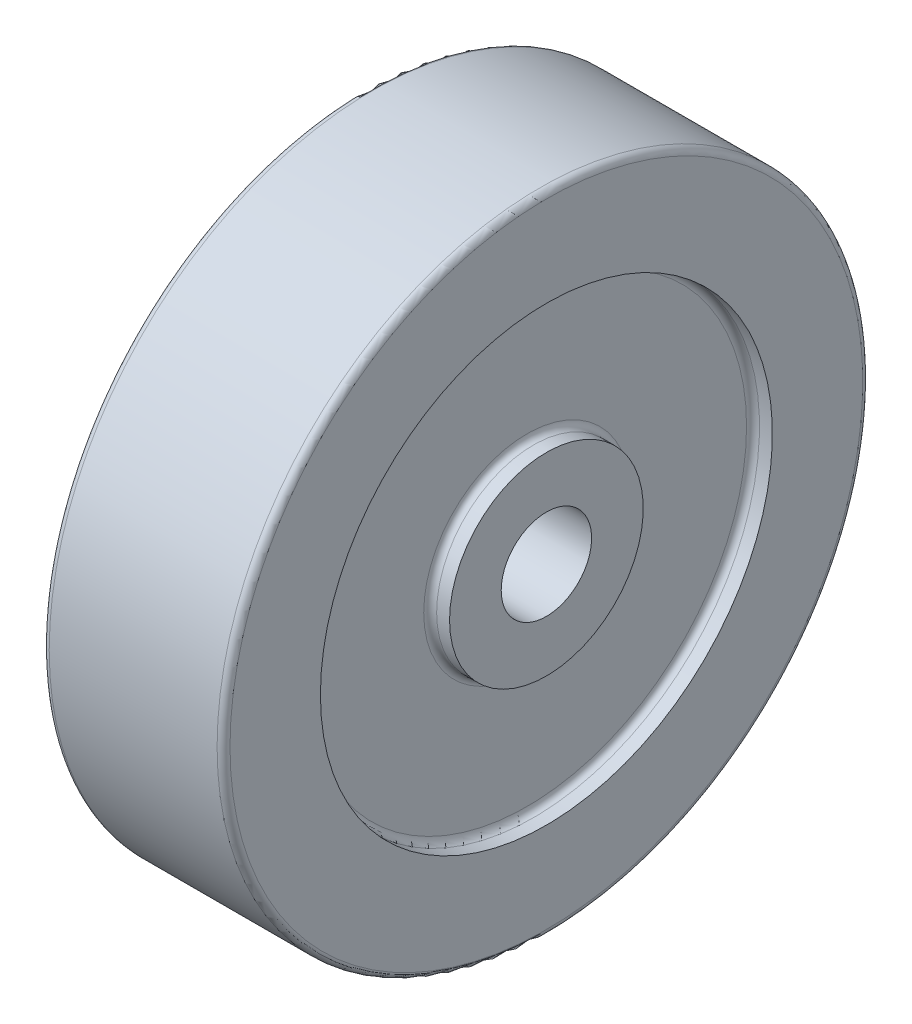
SolidWorks part; units mm, degrees
ref_plane "Front Plane" through (0, 0, 0) normal (0, 0, 1) x (1, 0, 0)
ref_plane "Top Plane" through (0, 0, 0) normal (0, 1, 0) x (1, 0, 0)
ref_plane "Right Plane" through (0, 0, 0) normal (1, 0, 0) x (0, 0, -1)
sketch "Sketch1" plane through (0, 0, 0) normal (0, 0, 1) x (1, 0, 0)
  line L0 (0, 0) -> (0, 64.5551) construction
  line L1 (0, 0) -> (69.5484, 0) construction
  line L2 (14, 7) -> (14, 15)
  line L6 (14, 35) -> (14, 50)
  line L7 (-14, 35) -> (-14, 50)
  line L11 (-14, 7) -> (-14, 15)
  line L12 (-14, 50) -> (14, 50)
  line L13 (-14, 7) -> (14, 7)
  line L14 (-14, 35) -> (-11, 35)
  line L15 (-11, 35) -> (-11, 15)
  line L16 (-11, 15) -> (-14, 15)
  line L17 (11, 15) -> (14, 15)
  line L18 (14, 35) -> (11, 35)
  line L19 (11, 35) -> (11, 15)
  dimension "D1" = 14
  dimension "D2" = 30
  dimension "D3" = 70
  dimension "D4" = 100
  dimension "D5" = 28
  dimension "D7" = 3
revolve "Revolve1" add sketch "Sketch1" angle 360 about L1
fillet "Fillet1" radius 1 6 edges at (11, 0, 35) (14, 0, 50) (-14, 0, 50) (11, 0, 15) (-11, 0, 15) (-11, 0, 35)
